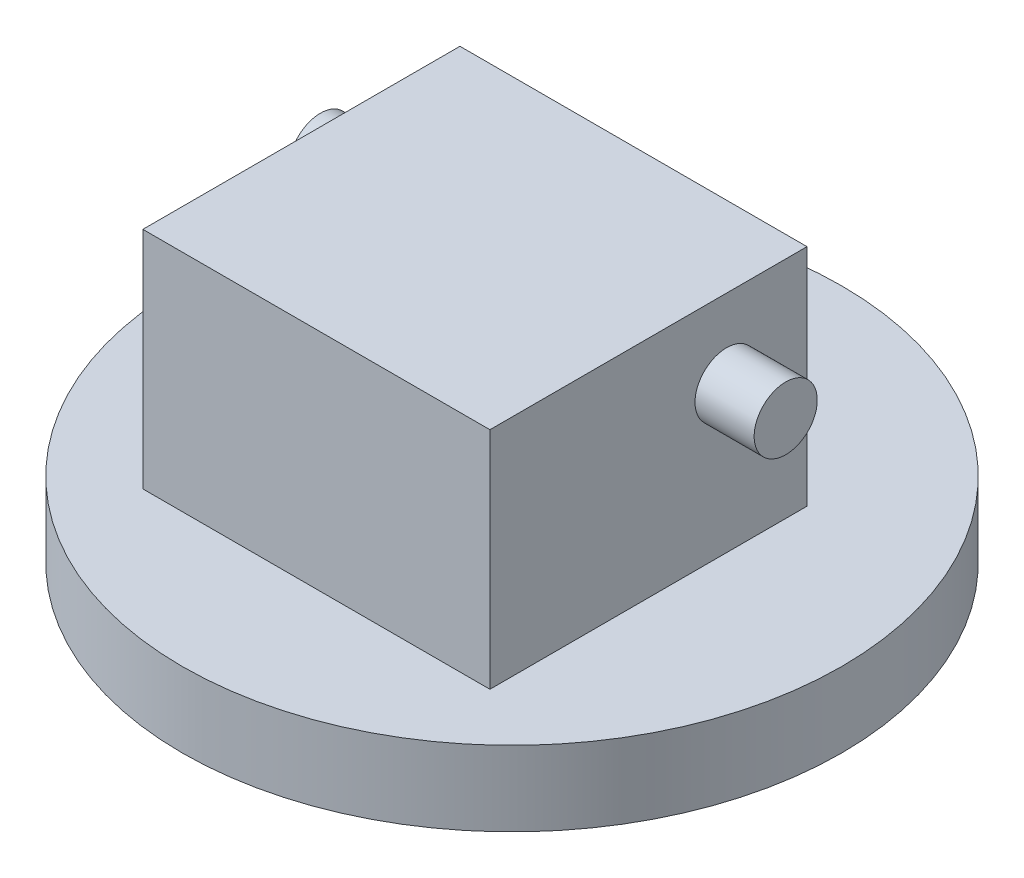
SolidWorks part; units mm, degrees
ref_plane "Front Plane" through (0, 0, 0) normal (0, 0, 1) x (1, 0, 0)
ref_plane "Top Plane" through (0, 0, 0) normal (0, 1, 0) x (1, 0, 0)
ref_plane "Right Plane" through (0, 0, 0) normal (1, 0, 0) x (0, 0, -1)
sketch "Sketch1" plane through (0, 0, 0) normal (0, 1, 0) x (1, 0, 0)
  circle A0 centre (0, 0) radius 41.8
  dimension "D1" = 83.6
extrude "Boss-Extrude1" add sketch "Sketch1" along normal blind 9.5
sketch "Sketch2" plane through (0, 9.5, 0) normal (0, 1, 0) x (1, 0, 0)
  line L0 (0, 0) -> (0, 41.8) construction
  line L1 (0, 68.2) -> (0, 15.4)
  line L2 (-22, 15.4) -> (22, 15.4)
  line L3 (22, 15.4) -> (22, -24.8)
  line L4 (22, -24.8) -> (-22, -24.8)
  line L5 (-22, 15.4) -> (-22, -24.8)
  circle A0 centre (0, 0) radius 41.8 construction
  point P8 (0, 41.8)
  point P12 (0, -24.8)
  dimension "D1" = 26.4
  dimension "D2" = 22
  dimension "D3" = 40.2
extrude "Boss-Extrude2" add sketch "Sketch2" along normal blind 28.5
sketch "Sketch3" plane through (22, 0, 0) normal (1, 0, 0) x (0, 0, -1)
  line L0 (-24.8, 28) -> (5.2, 28) construction
  line L1 (-24.8, 38) -> (-24.8, 9.5) construction
  line L2 (5.2, 28) -> (5.2, 9.5) construction
  line L3 (15.4, 9.5) -> (-24.8, 9.5) construction
  circle A1 centre (5.2, 28) radius 4
  dimension "D3" = 8
  dimension "D1" = 30
  dimension "D2" = 18.5
extrude "Boss-Extrude3" add sketch "Sketch3" along normal blind 7.5
mirror "Mirror2" about plane through (0, 0, 0) normal (1, 0, 0) of "Boss-Extrude3"
